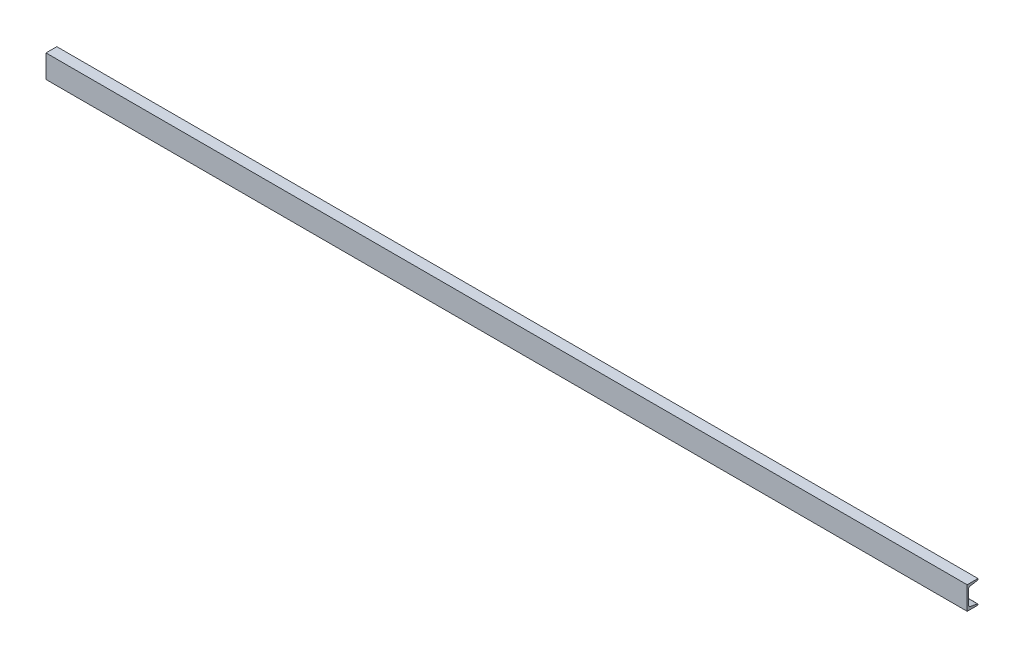
SolidWorks part; units mm, degrees
ref_plane "Front Plane" through (0, 0, 0) normal (0, 0, 1) x (1, 0, 0)
ref_plane "Top Plane" through (0, 0, 0) normal (0, 1, 0) x (1, 0, 0)
ref_plane "Right Plane" through (0, 0, 0) normal (1, 0, 0) x (0, 0, -1)
sketch "Sketch1" plane through (0, 0, 0) normal (0, 1, 0) x (1, 0, 0)
  line L0 (0, 0) -> (3048, 0)
  dimension "D1" = 3048
other "C channel C3X4.1(1)"
ref_plane "Plane1" through (0, -38.1, 0) normal (1, 0, 0) x (0, 0, -1)
sketch "Sketch11" plane through (0, -38.1, 0) normal (1, 0, 0) x (0, 0, -1)
  line L0 (0, 0) -> (0, 76.2)
  line L1 (0, 76.2) -> (35.814, 76.2)
  line L2 (0, 0) -> (35.814, 0)
  line L5 (35.814, 6.9342) -> (0, 6.9342) construction
  line L12 (4.318, 60.8314) -> (4.318, 15.3686)
  line L15 (35.814, 76.2) -> (35.814, 74.0423)
  line L16 (35.814, 0) -> (35.814, 2.1577)
  line L17 (10.0485, 67.5961) -> (33.6916, 71.5369)
  line L18 (10.0485, 8.6039) -> (33.6916, 4.6631)
  arc A9 (4.318, 15.3686) -> (10.0485, 8.6039) centre (11.176, 15.3686) ccw
  arc A10 (4.318, 60.8314) -> (10.0485, 67.5961) centre (11.176, 60.8314) cw
  arc A11 (35.814, 74.0423) -> (33.6916, 71.5369) centre (33.274, 74.0423) cw
  arc A12 (35.814, 2.1577) -> (33.6916, 4.6631) centre (33.274, 2.1577) ccw
  point P4 (17.907, 76.2)
  point P5 (4.318, 38.1)
  point P6 (17.907, 0)
  point P7 (0, 38.1)
  point P10 (0, 0)
  dimension "RI" = 6.858
  dimension "D2" = 9.463
  dimension "RA" = 2.54
  dimension "Depth" = 76.2
  dimension "BF" = 35.814
  dimension "TW" = 4.318
  dimension "flange" = 2.1577
  dimension "TF" = 6.9342
